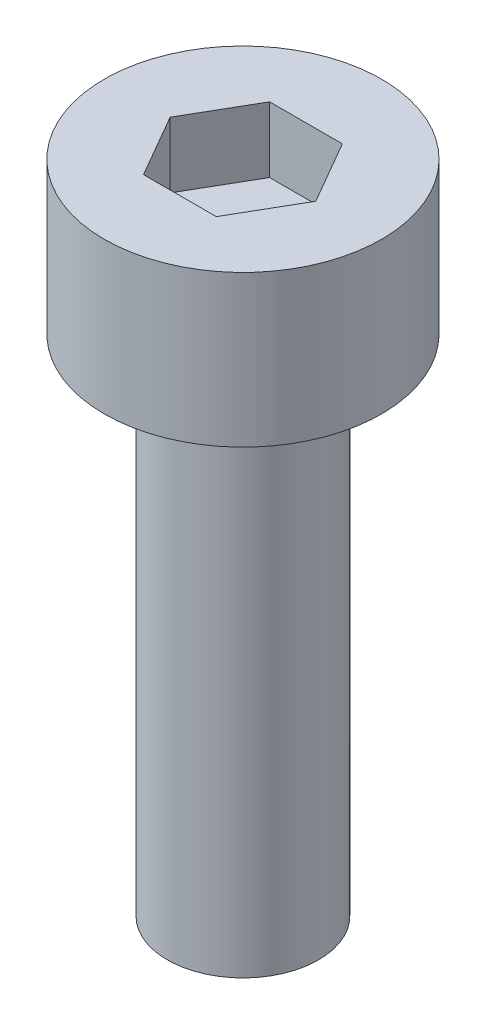
SolidWorks part; units mm, degrees
material "AISI 304"
ref_plane "前视基准面" through (0, 0, 0) normal (0, 0, 1) x (1, 0, 0)
ref_plane "上视基准面" through (0, 0, 0) normal (0, 1, 0) x (1, 0, 0)
ref_plane "右视基准面" through (0, 0, 0) normal (1, 0, 0) x (0, 0, -1)
sketch "草图1" plane through (0, 0, 0) normal (0, 1, 0) x (1, 0, 0)
  circle A0 centre (0, 0) radius 2.75
  dimension "D1" = 5.5
extrude "杯头" add sketch "草图1" along normal blind 3
sketch "草图2" plane through (0, 3, 0) normal (0, 1, 0) x (1, 0, 0)
  line L1 (1.4434, 0) -> (0.7217, 1.25)
  line L2 (0.7217, 1.25) -> (-0.7217, 1.25)
  line L3 (-0.7217, 1.25) -> (-1.4434, 0)
  line L4 (-1.4434, 0) -> (-0.7217, -1.25)
  line L5 (-0.7217, -1.25) -> (0.7217, -1.25)
  line L6 (0.7217, -1.25) -> (1.4434, 0)
  circle A0 centre (0, 0) radius 1.25 construction
  dimension "D1" = 2.5
extrude "内六角口" cut sketch "草图2" against normal blind 1.3
sketch "草图3" plane through (0, 0, 0) normal (0, -1, 0) x (1, 0, 0)
  circle A0 centre (0, 0) radius 1.5
  dimension "D1" = 3
extrude "螺纹长" add sketch "草图3" along normal blind 10
